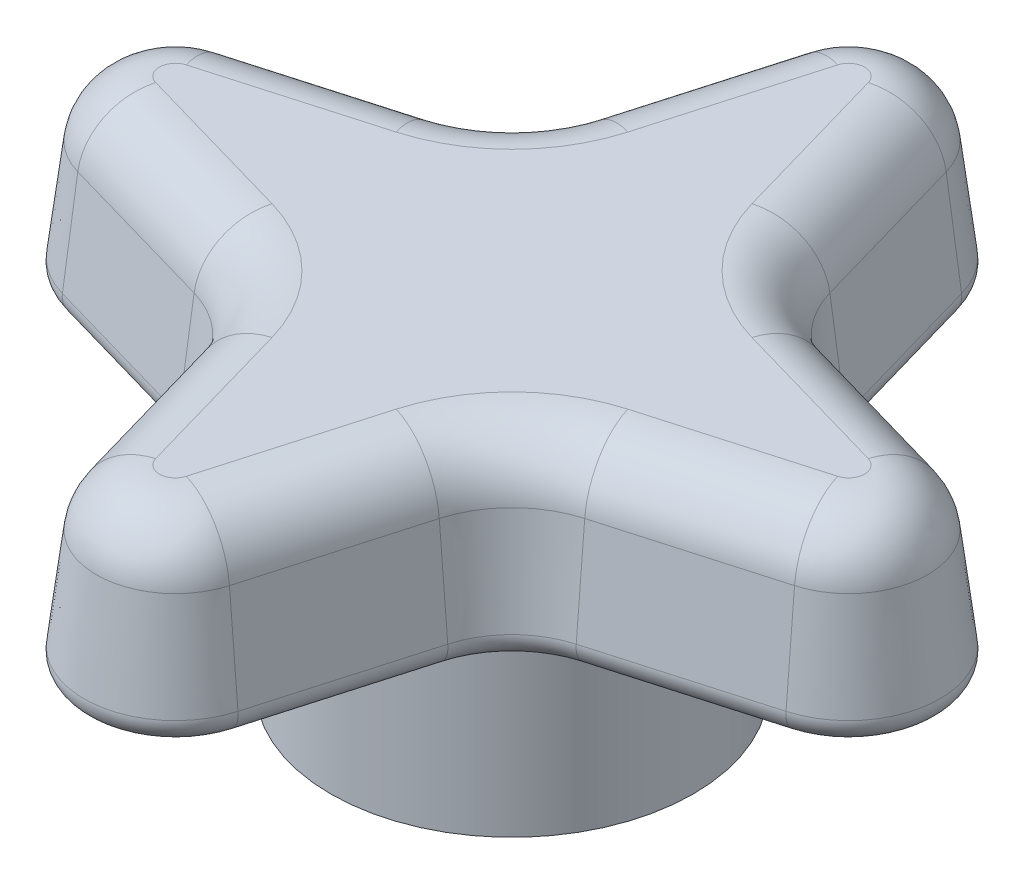
SolidWorks part; units mm, degrees
material "Plain Carbon Steel"
ref_plane "Front" through (0, 0, 0) normal (0, 0, 1) x (1, 0, 0)
ref_plane "Top" through (0, 0, 0) normal (0, 1, 0) x (1, 0, 0)
ref_plane "Right" through (0, 0, 0) normal (1, 0, 0) x (0, 0, -1)
sketch "Sketch1" plane through (0, 0, 0) normal (0, 1, 0) x (1, 0, 0)
  line L0 (0, 27.0019) -> (0, -27.0019) construction
  line L1 (-27.0019, 0) -> (27.0019, 0) construction
  line L2 (3.175, 12.7) -> (4.8125, 6.9894)
  line L3 (12.7, 3.175) -> (6.9894, 4.8125)
  line L4 (0, 0) -> (48.4155, 48.4155) construction
  line L5 (-12.7, 3.175) -> (-6.9894, 4.8125)
  line L6 (-3.175, 12.7) -> (-4.8125, 6.9894)
  line L7 (-3.175, -12.7) -> (-4.8125, -6.9894)
  line L8 (-12.7, -3.175) -> (-6.9894, -4.8125)
  line L9 (12.7, -3.175) -> (6.9894, -4.8125)
  line L10 (3.175, -12.7) -> (4.8125, -6.9894)
  arc A0 (4.8125, 6.9894) -> (6.9894, 4.8125) centre (7.8645, 7.8645) ccw
  arc A1 (-4.8125, 6.9894) -> (-6.9894, 4.8125) centre (-7.8645, 7.8645) cw
  arc A2 (-4.8125, -6.9894) -> (-6.9894, -4.8125) centre (-7.8645, -7.8645) ccw
  arc A3 (4.8125, -6.9894) -> (6.9894, -4.8125) centre (7.8645, -7.8645) cw
  arc A4 (12.7, 3.175) -> (12.7, -3.175) centre (11.7896, 0) cw
  arc A5 (3.175, -12.7) -> (-3.175, -12.7) centre (0, -11.7896) cw
  arc A6 (-12.7, -3.175) -> (-12.7, 3.175) centre (-11.7896, 0) cw
  arc A7 (-3.175, 12.7) -> (3.175, 12.7) centre (0, 11.7896) cw
  dimension "D4" = 3.175
  dimension "D1" = 16
  dimension "D2" = 6.35
  dimension "D3" = 45
  dimension "D5" = 12.7
extrude "Extrude1" add sketch "Sketch1" along normal blind 6.35 draft 7
fillet "Fillet1" radius 2.2225 16 edges at (-14.3129, 6.35, 0) (-9.6298, 6.35, -3.2443) (-5.0681, 6.35, -5.0681) (-3.2443, 6.35, -9.6298) (0, 6.35, -14.3129) (3.2443, 6.35, -9.6298) (5.0681, 6.35, -5.0681) (9.6298, 6.35, -3.2443) (14.3129, 6.35, 0) (9.6298, 6.35, 3.2443) (5.0681, 6.35, 5.0681) (3.2443, 6.35, 9.6298) (0, 6.35, 14.3129) (-3.2443, 6.35, 9.6298) (-5.0681, 6.35, 5.0681) (-9.6298, 6.35, 3.2443)
sketch "Sketch2" plane through (0, 0, 0) normal (0, -1, 0) x (1, 0, 0)
  circle A0 centre (0, 0) radius 6.35
  circle A1 centre (0, 0) radius 4.7625
  dimension "D1" = 12.7
  dimension "D2" = 9.525
extrude "Extrude2" add sketch "Sketch2" along normal blind 6.35
fillet "Fillet2" radius 0.762 16 edges at (-3.9938, 0, -9.8447) (-5.6194, 0, -5.6194) (-9.8447, 0, -3.9938) (-15.0925, 0, 0) (-9.8447, 0, 3.9938) (-5.6194, 0, 5.6194) (-3.9938, 0, 9.8447) (0, 0, 15.0925) (3.9938, 0, 9.8447) (5.6194, 0, 5.6194) (9.8447, 0, 3.9938) (15.0925, 0, 0) (9.8447, 0, -3.9938) (5.6194, 0, -5.6194) (3.9938, 0, -9.8447) (0, 0, -15.0925)
